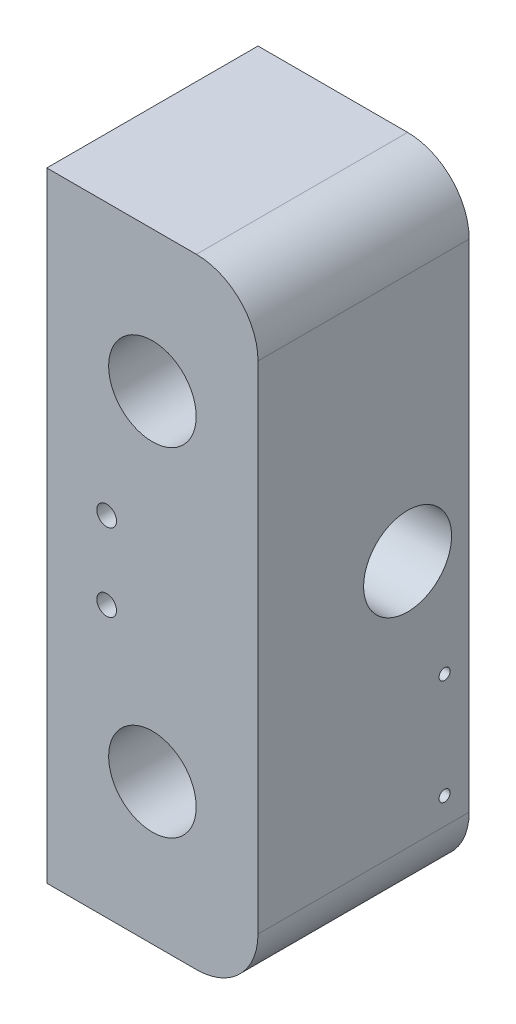
SolidWorks part; units mm, degrees
ref_plane "Front Plane" through (0, 0, 0) normal (0, 0, 1) x (1, 0, 0)
ref_plane "Top Plane" through (0, 0, 0) normal (0, 1, 0) x (1, 0, 0)
ref_plane "Right Plane" through (0, 0, 0) normal (1, 0, 0) x (0, 0, -1)
sketch "Sketch1" plane through (0, 0, 0) normal (0, 1, 0) x (1, 0, 0)
  line L1 (-19.05, -19.05) -> (19.05, -19.05)
  line L2 (-19.05, -19.05) -> (-19.05, 19.05)
  line L3 (-19.05, 19.05) -> (19.05, 19.05)
  line L4 (19.05, -19.05) -> (19.05, 19.05)
  line L5 (-19.05, -19.05) -> (19.05, 19.05) construction
  line L6 (-19.05, 19.05) -> (19.05, -19.05) construction
  point P0 (0, 0)
  dimension "D1" = 38.1
  dimension "D2" = 38.1
extrude "Boss-Extrude1" add sketch "Sketch1" along normal blind 111.76
sketch "Sketch2" plane through (0, 0, 19.05) normal (0, 0, 1) x (1, 0, 0)
  line L1 (-19.05, 0) -> (19.05, 0) construction
  line L3 (-19.05, 111.76) -> (-19.05, 0) construction
  circle A0 centre (0, 86.4) radius 7.9
  circle A1 centre (0, 25.4) radius 7.9
  dimension "D1" = 15.8
  dimension "D2" = 61
  dimension "D3" = 25.4
  dimension "D4" = 19.05
extrude "Cut-Extrude1" cut sketch "Sketch2" against normal through all both and the other way through all
sketch "Sketch3" plane through (0, 0, -19.05) normal (0, 0, -1) x (-1, 0, 0)
  line L0 (19.05, 44.45) -> (-1.27, 44.45)
  line L1 (19.05, 111.76) -> (19.05, 0) construction
  line L2 (-1.27, 44.45) -> (-1.27, 67.31)
  line L4 (19.05, 67.31) -> (19.05, 44.45)
  line L5 (-19.05, 111.76) -> (-19.05, 0) construction
  line L6 (-19.05, 55.88) -> (41.3589, 55.88) construction
  line L7 (19.05, 67.31) -> (-1.27, 67.31)
  point P11 (19.05, 55.88)
  point P12 (-1.27, 55.88)
  dimension "D1" = 11.43
  dimension "D2" = 20.32
extrude "Cut-Extrude2" cut sketch "Sketch3" against normal blind 22.225
sketch "Sketch5" plane through (19.05, 0, 0) normal (1, 0, 0) x (0, 0, -1)
  line L0 (19.05, 17.5) -> (19.05, 33.3) construction
  line L1 (19.05, 17.5) -> (19.05, 33.3)
  line L2 (19.05, 25.4) -> (-19.05, 25.4) construction
  line L3 (-19.05, 111.76) -> (-19.05, 0) construction
  circle A1 centre (14.605, 15.9) radius 1
  circle A2 centre (14.605, 34.9) radius 1
  dimension "D2" = 2
  dimension "D1" = 4.445
  dimension "D3" = 9.5
extrude "Cut-Extrude3" cut sketch "Sketch5" against normal blind 5.715 contours A2 | A1
sketch "Sketch6" plane through (1.27, 0, 0) normal (-1, 0, 0) x (0, 0, 1)
  line L0 (3.175, 67.31) -> (3.175, 44.45) construction
  line L1 (3.175, 67.31) -> (3.175, 44.45)
  line L2 (3.175, 44.45) -> (-19.05, 44.45) construction
  line L3 (3.175, 44.45) -> (-19.05, 44.45)
  circle A0 centre (-7.9375, 55.88) radius 7.9375
  point P4 (3.175, 55.88)
  point P5 (-7.9375, 44.45)
  dimension "D1" = 15.875
extrude "Cut-Extrude4" cut sketch "Sketch6" against normal through all both and the other way through all contours A0
sketch "Sketch7" plane through (0, 0, 3.175) normal (0, 0, -1) x (-1, 0, 0)
  line L0 (-1.27, 44.45) -> (19.05, 44.45) construction
  line L1 (-1.27, 67.31) -> (-1.27, 44.45) construction
  line L2 (-1.27, 44.45) -> (19.05, 44.45)
  line L3 (-1.27, 67.31) -> (-1.27, 44.45)
  line L4 (-1.27, 55.88) -> (26.2328, 55.88) construction
  circle A0 centre (8.255, 48.895) radius 1.778
  circle A1 centre (8.255, 62.865) radius 1.778
  dimension "D3" = 3.556
  dimension "D1" = 6.985
  dimension "D2" = 9.525
extrude "Cut-Extrude5" cut sketch "Sketch7" against normal through all both and the other way through all contours A1 | A0
sketch "Sketch8" plane through (0, 0, -19.05) normal (0, 0, -1) x (-1, 0, 0)
  line L0 (-19.05, 16.9) -> (-19.05, 14.9) construction
  line L1 (-19.05, 16.9) -> (-19.05, 14.9)
  line L2 (-1.27, 67.31) -> (-1.27, 44.45) construction
  line L3 (19.05, 44.45) -> (19.05, 0) construction
  line L4 (-19.05, 0) -> (19.05, 0) construction
  line L5 (-1.27, 67.31) -> (-1.27, 44.45)
  line L6 (19.05, 44.45) -> (19.05, 0)
  line L7 (-19.05, 0) -> (19.05, 0)
  line L8 (-1.27, 55.88) -> (-37.8967, 55.88) construction
  line L9 (-19.05, 111.76) -> (-19.05, 0) construction
  line L10 (-19.05, 111.76) -> (-19.05, 0)
  line L11 (-19.05, 111.76) -> (19.05, 111.76)
  arc A0 (-19.05, 11.1125) -> (-7.9375, 0) centre (-7.9375, 11.1125) ccw
  arc A1 (-19.05, 100.6475) -> (-7.9375, 111.76) centre (-7.9375, 100.6475) cw
  line M10 (-19.05, 111.76) -> (-19.05, 0)
  line M11 (-19.05, 0) -> (19.05, 0)
  dimension "D1" = 22.225
extrude "Cut-Extrude6" cut sketch "Sketch8" against normal through all both and the other way through all contours A0 L10 M11 | A1 L11 M10
equation "\"8mm hole\" = 8.4mm"
equation "\"22mm hole\"= 23mm"
equation "\"15mm hole\"= 15.8mm"
equation "\"bed height offset\"= 3mm"
equation "\"motor width\"= 42.5mm"
equation "\"D1@Sketch2\"=\"15mm hole\""
equation "\"D1@Boss-Extrude1\"=\"15mm hole\" + 2in"
